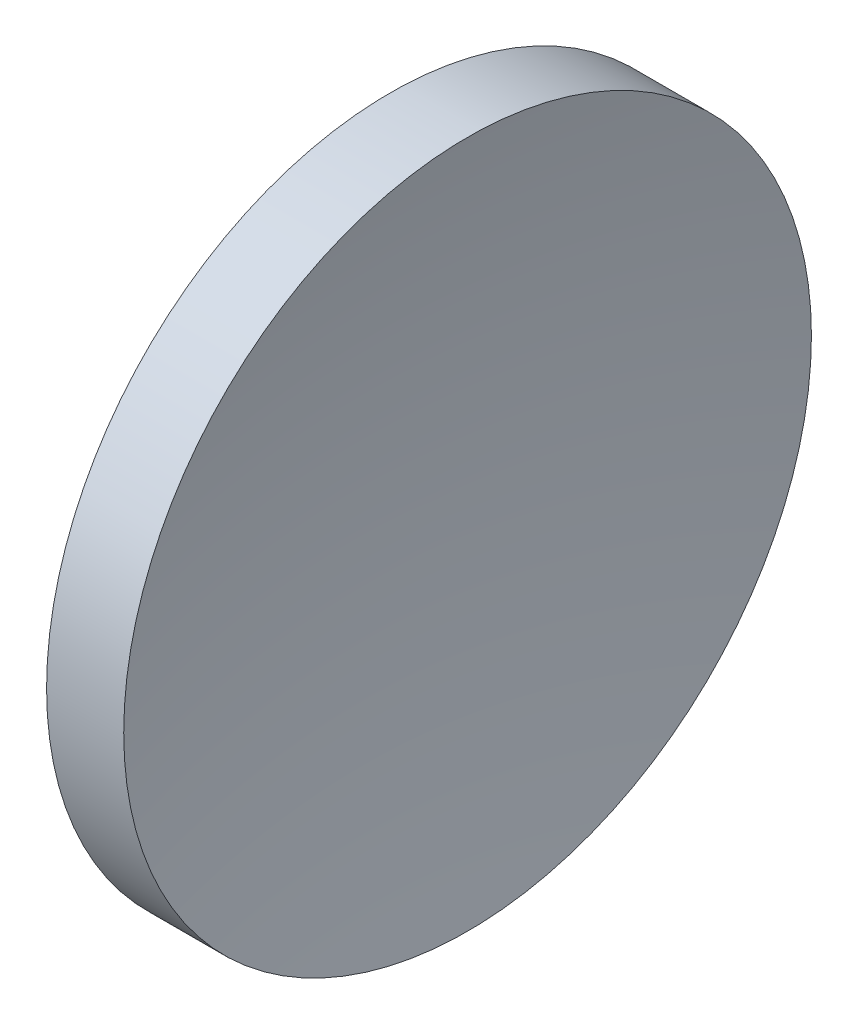
SolidWorks part; units mm, degrees
ref_plane "前视基准面" through (0, 0, 0) normal (0, 0, 1) x (1, 0, 0)
ref_plane "上视基准面" through (0, 0, 0) normal (0, 1, 0) x (1, 0, 0)
ref_plane "右视基准面" through (0, 0, 0) normal (1, 0, 0) x (0, 0, -1)
sketch "草图1" plane through (0, 0, 0) normal (0, 0, 1) x (1, 0, 0)
  line L0 (105.6218, 65.1556) -> (137.1869, 65.1556) construction
  line L1 (113.9119, 65.1556) -> (113.9119, 85.1556)
  line L2 (113.9119, 85.1556) -> (118.3986, 85.1556)
  line L3 (116.4119, 65.1556) -> (113.9119, 65.1556)
  arc A0 (118.3986, 85.1556) -> (116.4119, 65.1556) centre (219.6918, 64.9953) ccw
revolve "旋转1" add sketch "草图1" angle 360 about L0
